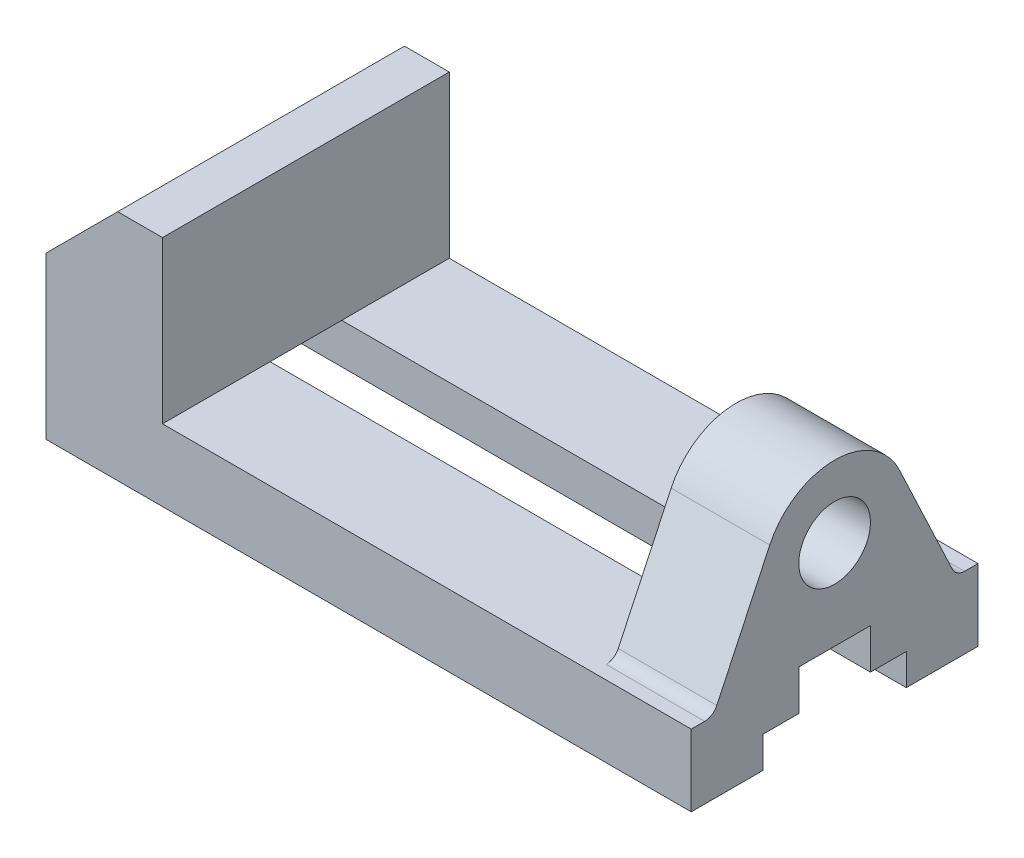
SolidWorks part; units mm, degrees
ref_plane "Front Plane" through (0, 0, 0) normal (0, 0, 1) x (1, 0, 0)
ref_plane "Top Plane" through (0, 0, 0) normal (0, 1, 0) x (1, 0, 0)
ref_plane "Right Plane" through (0, 0, 0) normal (1, 0, 0) x (0, 0, -1)
sketch "Sketch1" plane through (0, 0, 0) normal (0, 0, 1) x (1, 0, 0)
  line L0 (-72, 8) -> (-72, 28)
  line L1 (-46, 8) -> (72, 8)
  line L2 (-72, 8) -> (-72, -8)
  line L3 (-72, -8) -> (72, -8)
  line L4 (72, 8) -> (72, -8)
  line L7 (-46, 44) -> (-46, 8)
  line L8 (-46, 44) -> (-56, 44)
  line L9 (-56, 44) -> (-72, 28)
  point P0 (0, 0)
extrude "Boss-Extrude1" add sketch "Sketch1" along normal mid plane 64
sketch "Sketch2" plane through (72, 0, 0) normal (1, 0, 0) x (0, 0, -1)
  line L0 (-32, -8) -> (32, -8) construction
  line L1 (-16, -8) -> (-16, -1)
  line L2 (-16, -1) -> (-8, -1)
  line L3 (16, -8) -> (16, -1)
  line L4 (16, -1) -> (8, -1)
  line L5 (8, -1) -> (8, 8)
  line L6 (-32, 8) -> (32, 8) construction
  line L7 (-8, -1) -> (-8, 8)
  line L8 (-8, 8) -> (8, 8)
  line L9 (-16, -8) -> (16, -8)
  point P1 (0, -1)
  dimension "D1" = 32
  dimension "D3" = 7
  dimension "D4" = 7
extrude "Cut-Extrude1" cut sketch "Sketch2" against normal up to next
sketch "Sketch4" plane through (72, 0, 0) normal (1, 0, 0) x (0, 0, -1)
  line L0 (16, -8) -> (32, -8) construction
  line L1 (-26.2856, 9.7225) -> (-14.4768, 34.8134)
  line L4 (0, 0) -> (0, 51.2542) construction
  line L5 (26.2856, 9.7225) -> (14.4768, 34.8134)
  line L6 (-32, 8) -> (-8, 8) construction
  line L7 (8, 8) -> (32, 8) construction
  line L8 (-32, 8) -> (32, 8)
  circle A1 centre (0, 28) radius 16
  circle A2 centre (0, 28) radius 8
  arc A4 (-26.2856, 9.7225) -> (-29, 8) centre (-29, 11) cw
  arc A5 (26.2856, 9.7225) -> (29, 8) centre (29, 11) ccw
  dimension "D2" = 32
  dimension "D3" = 16
  dimension "D1" = 36
extrude "Boss-Extrude3" add sketch "Sketch4" against normal blind 22 contours L8 L4 A1 L1 A4 | L4 L8 A5 L5 A1 | L4 A1 A2 | A1 L4 A2
